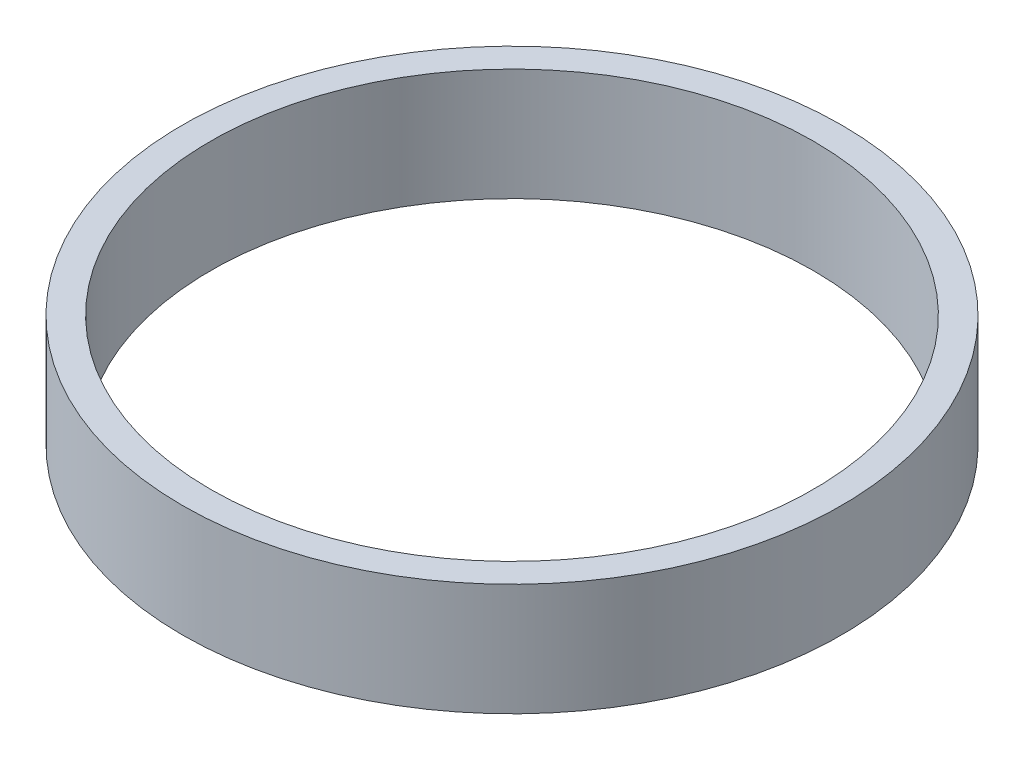
SolidWorks part; units mm, degrees
ref_plane "Front Plane" through (0, 0, 0) normal (0, 0, 1) x (1, 0, 0)
ref_plane "Top Plane" through (0, 0, 0) normal (0, 1, 0) x (1, 0, 0)
ref_plane "Right Plane" through (0, 0, 0) normal (1, 0, 0) x (0, 0, -1)
sketch "Sketch1" plane through (0, 0, 0) normal (0, 1, 0) x (1, 0, 0)
  circle A0 centre (0, 0) radius 1193.8
  circle A1 centre (0, 0) radius 1092.2
  dimension "D1" = 2387.6
  dimension "D2" = 2184.4
extrude "Boss-Extrude1" add sketch "Sketch1" along normal mid plane 406.4
